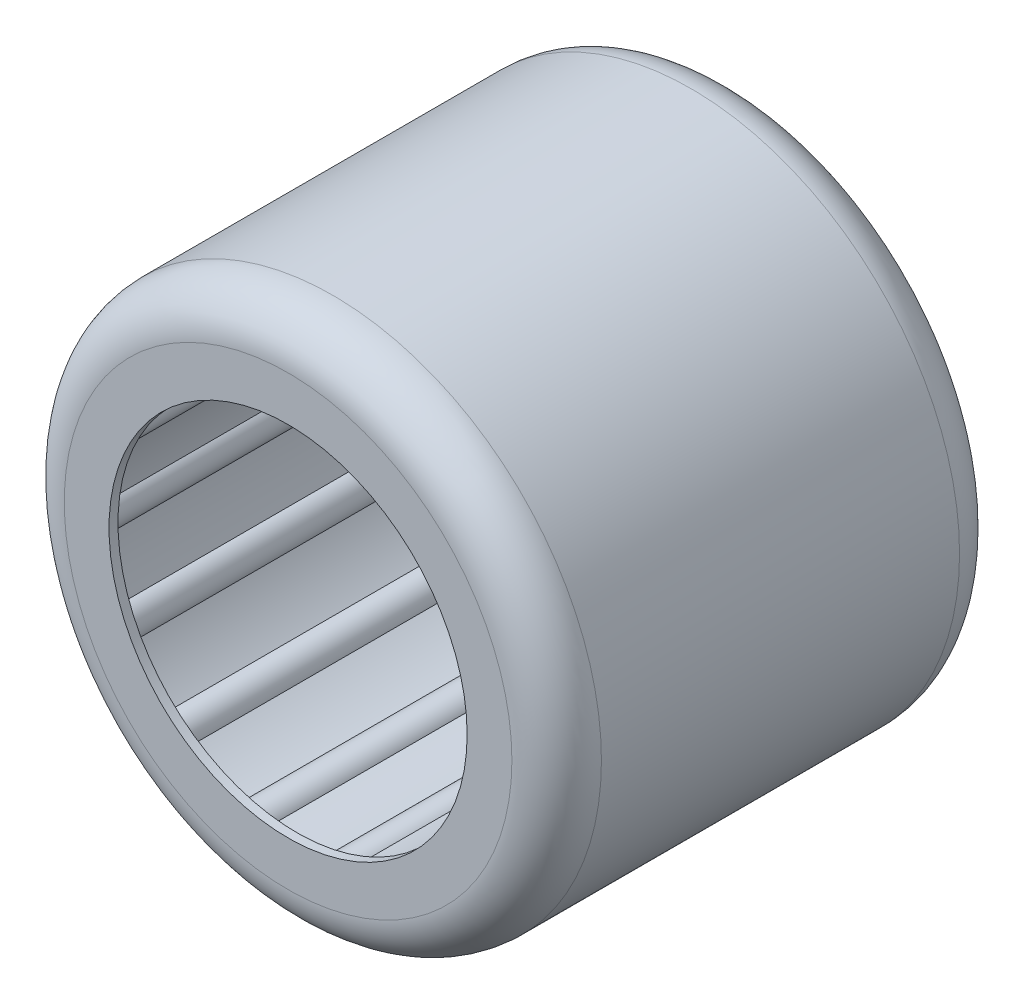
SolidWorks part; units mm, degrees
ref_plane "Plan de face" through (0, 0, 0) normal (0, 0, 1) x (1, 0, 0)
ref_plane "Plan de dessus" through (0, 0, 0) normal (0, 1, 0) x (1, 0, 0)
ref_plane "Plan de droite" through (0, 0, 0) normal (1, 0, 0) x (0, 0, -1)
sketch "Esquisse1" plane through (0, 0, 0) normal (0, 0, 1) x (1, 0, 0)
  circle A0 centre (0, 0) radius 6
  point P3 (0, 0)
extrude "Boss.-Extru.2" add sketch "Esquisse1" along normal blind 10 contours A0
fillet "Congé2" radius 1 2 edges at (6, 0, 0) (6, 0, 10)
sketch "Esquisse5" plane through (0, 0, 10) normal (0, 0, 1) x (1, 0, 0)
  circle A0 centre (0, 0) radius 4
extrude "Enlèv. mat.-Extru.2" cut sketch "Esquisse5" against normal through all contours A0
shell "Coque5" thickness 0.2
sketch "Esquisse7" plane through (0, 0, 0.2) normal (0, 0, 1) x (1, 0, 0)
  circle A2 centre (-4.5, 0) radius 0.4326
  circle A3 centre (-4.0544, 1.9525) radius 0.4326
  circle A4 centre (-2.8057, 3.5182) radius 0.4326
  circle A5 centre (-1.0013, 4.3872) radius 0.4326
  circle A6 centre (1.0013, 4.3872) radius 0.4326
  circle A7 centre (2.8057, 3.5182) radius 0.4326
  circle A8 centre (4.0544, 1.9525) radius 0.4326
  circle A9 centre (4.5, 0) radius 0.4326
  circle A10 centre (4.0544, -1.9525) radius 0.4326
  circle A11 centre (2.8057, -3.5182) radius 0.4326
  circle A12 centre (1.0013, -4.3872) radius 0.4326
  circle A13 centre (-1.0013, -4.3872) radius 0.4326
  circle A14 centre (-2.8057, -3.5182) radius 0.4326
  circle A15 centre (-4.0544, -1.9525) radius 0.4326
  point P0 (0, 0)
  point P38 (0, 0)
  dimension "D1" = 14
sketch "Esquisse12" plane through (0, 0, 0.2) normal (0, 0, 1) x (1, 0, 0)
  arc A0 (-3.9409, 1.535) -> (-4.2166, 0.3269) centre (0, 0) ccw
  arc A1 (-4.089, 1.5212) -> (-4.3441, 0.4036) centre (0, 0) ccw
  circle A2 centre (-4.0544, 1.9525) radius 0.4326 construction
  circle A3 centre (-4.5, 0) radius 0.4326 construction
  circle A4 centre (-4.0544, -1.9525) radius 0.4326 construction
  circle A5 centre (-2.8057, -3.5182) radius 0.4326 construction
  circle A6 centre (-1.0013, -4.3872) radius 0.4326 construction
  circle A7 centre (1.0013, -4.3872) radius 0.4326 construction
  circle A8 centre (2.8057, -3.5182) radius 0.4326 construction
  circle A9 centre (4.0544, -1.9525) radius 0.4326 construction
  circle A10 centre (4.5, 0) radius 0.4326 construction
  circle A11 centre (4.0544, 1.9525) radius 0.4326 construction
  circle A12 centre (2.8057, 3.5182) radius 0.4326 construction
  circle A13 centre (1.0013, 4.3872) radius 0.4326 construction
  circle A14 centre (-1.0013, 4.3872) radius 0.4326 construction
  circle A15 centre (-2.8057, 3.5182) radius 0.4326 construction
  arc A16 (-3.7388, 2.2485) -> (-4.089, 1.5212) centre (-4.0544, 1.9525) ccw
  arc A17 (-4.2166, -0.3269) -> (-4.2166, 0.3269) centre (-4.5, 0) ccw
  arc A18 (-3.6572, -2.1241) -> (-3.9409, -1.535) centre (-4.0544, -1.9525) ccw
  arc A19 (-3.024, -3.1447) -> (-2.393, -3.648) centre (-2.8057, -3.5182) ccw
  arc A20 (-0.6196, -4.1837) -> (-1.257, -4.0382) centre (-1.0013, -4.3872) ccw
  arc A21 (0.5732, -4.325) -> (1.3601, -4.1454) centre (1.0013, -4.3872) ccw
  arc A22 (2.8846, -3.0929) -> (2.3734, -3.5005) centre (2.8057, -3.5182) ccw
  arc A23 (3.7388, -2.2485) -> (4.089, -1.5212) centre (4.0544, -1.9525) ccw
  arc A24 (4.2166, 0.3269) -> (4.2166, -0.3269) centre (4.5, 0) ccw
  arc A25 (3.6572, 2.1241) -> (3.9409, 1.535) centre (4.0544, 1.9525) ccw
  arc A26 (2.3734, 3.5005) -> (2.8846, 3.0929) centre (2.8057, 3.5182) ccw
  arc A27 (0.6196, 4.1837) -> (1.257, 4.0382) centre (1.0013, 4.3872) ccw
  arc A28 (-1.257, 4.0382) -> (-0.6196, 4.1837) centre (-1.0013, 4.3872) ccw
  arc A29 (-2.8846, 3.0929) -> (-2.3734, 3.5005) centre (-2.8057, 3.5182) ccw
  arc A30 (-2.8846, 3.0929) -> (-3.6572, 2.1241) centre (0, 0) ccw
  arc A31 (-3.024, 3.1447) -> (-3.7388, 2.2485) centre (0, 0) ccw
  arc A32 (-1.257, 4.0382) -> (-2.3734, 3.5005) centre (0, 0) ccw
  arc A33 (-1.3601, 4.1454) -> (-2.393, 3.648) centre (0, 0) ccw
  arc A34 (0.6196, 4.1837) -> (-0.6196, 4.1837) centre (0, 0) ccw
  arc A35 (0.5732, 4.325) -> (-0.5732, 4.325) centre (0, 0) ccw
  arc A36 (2.3734, 3.5005) -> (1.257, 4.0382) centre (0, 0) ccw
  arc A37 (2.393, 3.648) -> (1.3601, 4.1454) centre (0, 0) ccw
  arc A38 (3.6572, 2.1241) -> (2.8846, 3.0929) centre (0, 0) ccw
  arc A39 (3.7388, 2.2485) -> (3.024, 3.1447) centre (0, 0) ccw
  arc A40 (4.2166, 0.3269) -> (3.9409, 1.535) centre (0, 0) ccw
  arc A41 (4.3441, 0.4036) -> (4.089, 1.5212) centre (0, 0) ccw
  arc A42 (4.089, -1.5212) -> (4.3441, -0.4036) centre (0, 0) ccw
  arc A43 (3.9409, -1.535) -> (4.2166, -0.3269) centre (0, 0) ccw
  arc A44 (3.024, -3.1447) -> (3.7388, -2.2485) centre (0, 0) ccw
  arc A45 (2.8846, -3.0929) -> (3.6572, -2.1241) centre (0, 0) ccw
  arc A46 (1.3601, -4.1454) -> (2.393, -3.648) centre (0, 0) ccw
  arc A47 (1.257, -4.0382) -> (2.3734, -3.5005) centre (0, 0) ccw
  arc A48 (-0.5732, -4.325) -> (0.5732, -4.325) centre (0, 0) ccw
  arc A49 (-0.6196, -4.1837) -> (0.6196, -4.1837) centre (0, 0) ccw
  arc A50 (-2.393, -3.648) -> (-1.3601, -4.1454) centre (0, 0) ccw
  arc A51 (-2.3734, -3.5005) -> (-1.257, -4.0382) centre (0, 0) ccw
  arc A52 (-3.7388, -2.2485) -> (-3.024, -3.1447) centre (0, 0) ccw
  arc A53 (-3.6572, -2.1241) -> (-2.8846, -3.0929) centre (0, 0) ccw
  arc A54 (-4.3441, -0.4036) -> (-4.089, -1.5212) centre (0, 0) ccw
  arc A55 (-4.2166, -0.3269) -> (-3.9409, -1.535) centre (0, 0) ccw
  arc A56 (-2.393, 3.648) -> (-3.024, 3.1447) centre (-2.8057, 3.5182) ccw
  arc A57 (-0.5732, 4.325) -> (-1.3601, 4.1454) centre (-1.0013, 4.3872) ccw
  arc A58 (1.3601, 4.1454) -> (0.5732, 4.325) centre (1.0013, 4.3872) ccw
  arc A59 (3.024, 3.1447) -> (2.393, 3.648) centre (2.8057, 3.5182) ccw
  arc A60 (4.089, 1.5212) -> (3.7388, 2.2485) centre (4.0544, 1.9525) ccw
  arc A61 (3.9409, -1.535) -> (3.6572, -2.1241) centre (4.0544, -1.9525) ccw
  arc A62 (2.393, -3.648) -> (3.024, -3.1447) centre (2.8057, -3.5182) ccw
  arc A63 (4.3441, -0.4036) -> (4.3441, 0.4036) centre (4.5, 0) ccw
  arc A64 (1.257, -4.0382) -> (0.6196, -4.1837) centre (1.0013, -4.3872) ccw
  arc A65 (-1.3601, -4.1454) -> (-0.5732, -4.325) centre (-1.0013, -4.3872) ccw
  arc A66 (-2.3734, -3.5005) -> (-2.8846, -3.0929) centre (-2.8057, -3.5182) ccw
  arc A67 (-4.089, -1.5212) -> (-3.7388, -2.2485) centre (-4.0544, -1.9525) ccw
  arc A68 (-4.3441, 0.4036) -> (-4.3441, -0.4036) centre (-4.5, 0) ccw
  arc A69 (-3.9409, 1.535) -> (-3.6572, 2.1241) centre (-4.0544, 1.9525) ccw
extrude "Boss.-Extru.5" add sketch "Esquisse12" along normal through all
